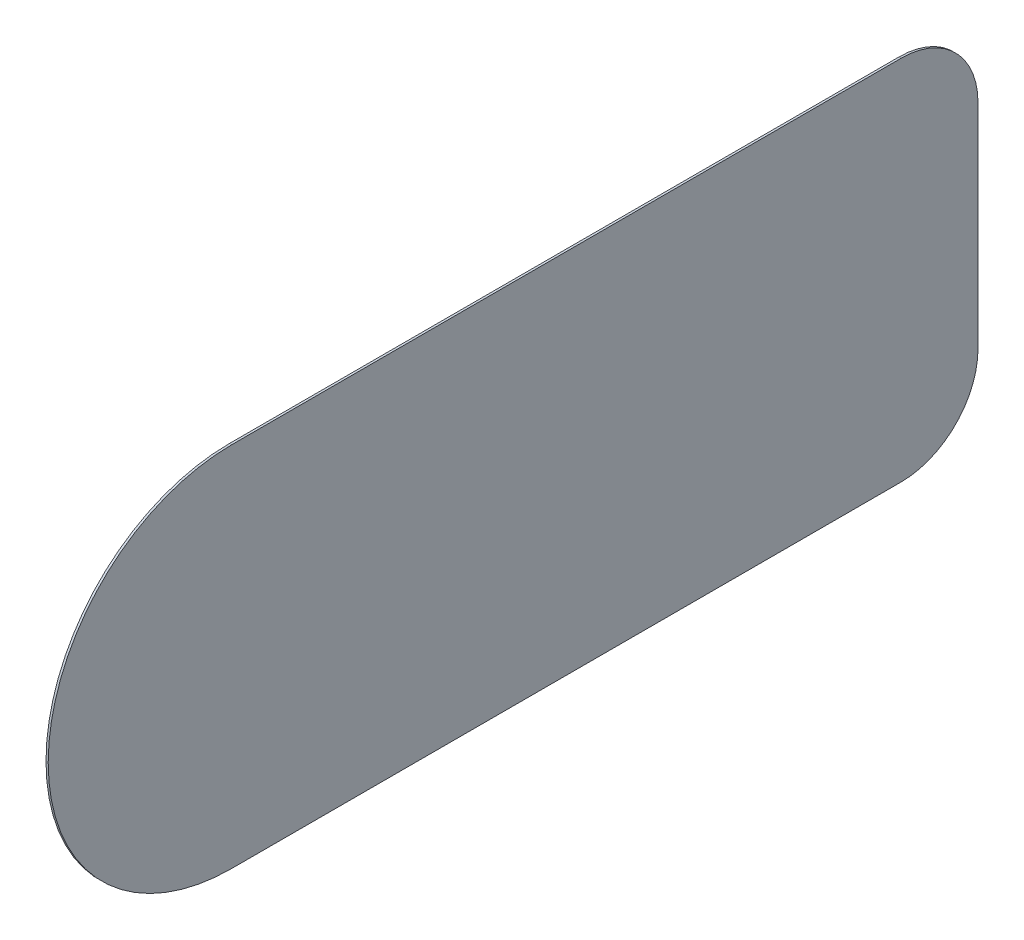
SolidWorks part; units mm, degrees
ref_plane "Front Plane" through (0, 0, 0) normal (0, 0, 1) x (1, 0, 0)
ref_plane "Top Plane" through (0, 0, 0) normal (0, 1, 0) x (1, 0, 0)
ref_plane "Right Plane" through (0, 0, 0) normal (1, 0, 0) x (0, 0, -1)
sketch "Sketch2" plane through (0, 0, 0) normal (1, 0, 0) x (0, 0, -1)
  line L0 (0, 0) -> (3050, 0)
  line L1 (3400, 350) -> (3400, 1322)
  line L2 (3050, 1672) -> (0, 1672)
  arc A0 (3050, 0) -> (3400, 350) centre (3050, 350) ccw
  arc A1 (3400, 1322) -> (3050, 1672) centre (3050, 1322) ccw
  arc A2 (0, 1672) -> (0, 0) centre (0, 836) ccw
  dimension "D1" = 3050
extrude "Boss-Extrude1" add sketch "Sketch2" along normal blind 10
